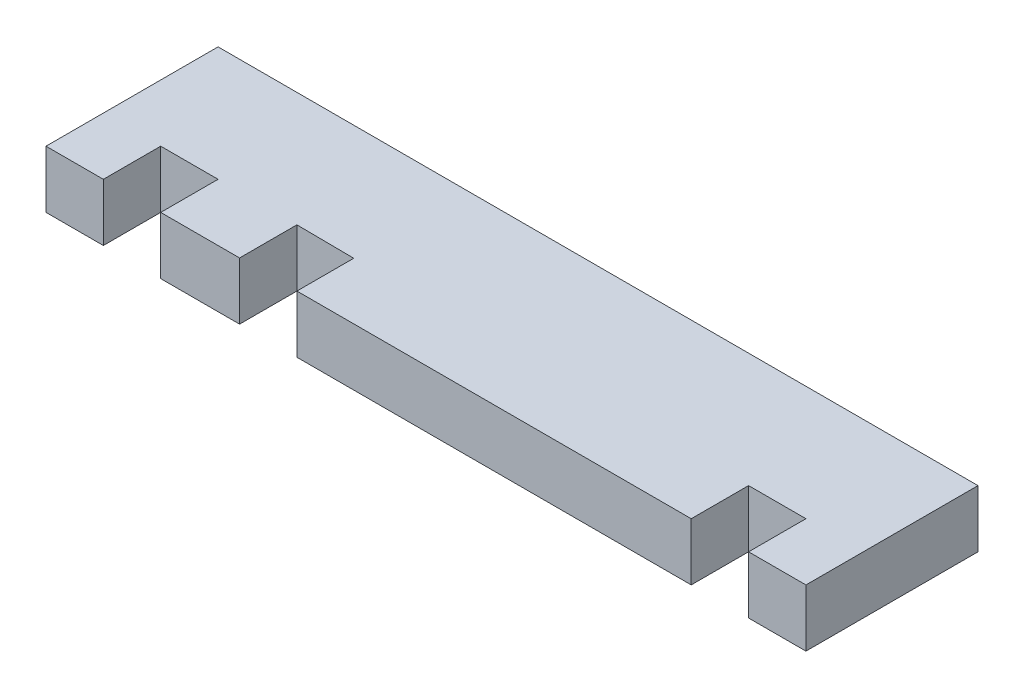
SolidWorks part; units mm, degrees
ref_plane "Front Plane" through (0, 0, 0) normal (0, 0, 1) x (1, 0, 0)
ref_plane "Top Plane" through (0, 0, 0) normal (0, 1, 0) x (1, 0, 0)
ref_plane "Right Plane" through (0, 0, 0) normal (1, 0, 0) x (0, 0, -1)
sketch "Sketch1" plane through (0, 0, 0) normal (0, 1, 0) x (1, 0, 0)
  line L0 (-26.5, 0) -> (26.5, 0) construction
  line L1 (-26.5, -6) -> (26.5, -6) construction
  line L2 (-26.5, -6) -> (-26.5, 6) construction
  line L3 (-26.5, 6) -> (26.5, 6)
  line L4 (26.5, -6) -> (26.5, 6) construction
  line L5 (-26.5, -6) -> (26.5, 6) construction
  line L6 (-26.5, 6) -> (26.5, -6) construction
  line L7 (-26.5, 6) -> (-26.5, -6)
  line L8 (-26.5, -6) -> (-22.5, -6)
  line L9 (-22.5, -6) -> (-22.5, -2)
  line L10 (-22.5, -2) -> (-18.5, -2)
  line L11 (-18.5, -2) -> (-18.5, -6)
  line L17 (-12.9998, -6) -> (-12.9998, -2)
  line L18 (-12.9998, -2) -> (-9, -2.0377)
  line L19 (-9, -2.0377) -> (-9, -6)
  line L25 (18.5, -6) -> (18.5, -2)
  line L26 (18.5, -2) -> (22.5, -2)
  line L27 (22.5, -2) -> (22.5, -6)
  line L28 (22.5, -6) -> (26.5, -6)
  line L29 (26.5, -6) -> (26.5, 6)
  line L30 (-18.5, -6) -> (-12.9998, -6)
  line L31 (18.5, -6) -> (-9, -6)
  line L32 (-26.5, -2) -> (26.5, -2) construction
  point P0 (0, 0)
  dimension "D1" = 12
  dimension "D3" = 4
  dimension "D2" = 13.5
  dimension "D4" = 31.5
  dimension "D5" = 4
extrude "Boss-Extrude1" add sketch "Sketch1" along normal blind 4
equation "\"m3_hole\"= 3.5"
equation "\"m3_washer\"= 7.3"
equation "\"m3_nut\"= 5.3"
equation "\"plywood_thickness\" = 4.0"
equation "\"guide_width\"= 10.0"
equation "\"guide_length\"= 65.0"
equation "\"guide_tab_length\" = 10.0"
equation "\"guide_tab_width\" = 9.0"
equation "\"guide_thickness\" = 12.0"
equation "\"grinder_od\"= 52.0"
equation "\"grinder_id\"= 45.5"
equation "\"grinder_adjust_od\" = 58.0"
equation "\"funnel_width_from_adjust_ring\" = 13.0"
equation "\"drill_contact_diameter_small\" = 24.0"
equation "\"drill_contact_diameter_medium\" = 28.0"
equation "\"drill_contact_diameter_large\" = 39.0"
equation "\"drill_contact_diameter_tab\" = 31.0"
equation "\"drill_contact_ow_tab\" = 14.5"
equation "\"drill_contact_iw_tab\" = 8.7"
equation "\"drill_contact_small_height\" = 15.5"
equation "\"drill_contact_large_height\" = 34.5"
equation "\"plywood_peg_length\" = 40.0"
equation "\"plywood_peg_width\" = 8.0"
equation "\"D1@Sketch1\"=\"plywood_thickness\"*3"
equation "\"D3@Sketch1\"=\"plywood_thickness\""
equation "\"D5@Sketch1\"=\"plywood_thickness\""
